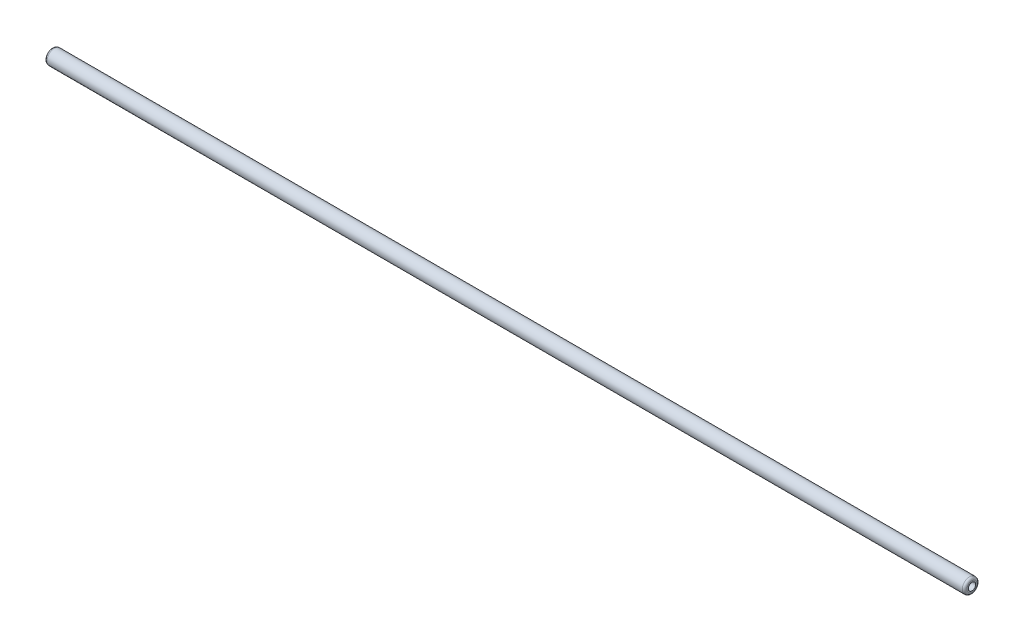
SolidWorks part; units mm, degrees
material "Alloy Steel"
ref_plane "Front Plane" through (0, 0, 0) normal (0, 0, 1) x (1, 0, 0)
ref_plane "Top Plane" through (0, 0, 0) normal (0, 1, 0) x (1, 0, 0)
ref_plane "Right Plane" through (0, 0, 0) normal (1, 0, 0) x (0, 0, -1)
sketch "스케치1" plane through (0, 0, 0) normal (0, 1, 0) x (1, 0, 0)
  circle A0 centre (0, 0) radius 7.9375
  circle A1 centre (0, 0) radius 3.975
  dimension "D1" = 15.875
  dimension "D2" = 7.95
extrude "보스-돌출1" add sketch "스케치1" along normal mid plane 987.298
fillet "필렛1" radius 2.5 2 edges at (0, 493.649, 7.9375) (0, -493.649, 7.9375)
move or copy body "바디-이동/복사1" bodies to move or copy 101 copy no rotation origin (0, 0, 0) rotation axis (0, 0, 1) rotation angle 90
